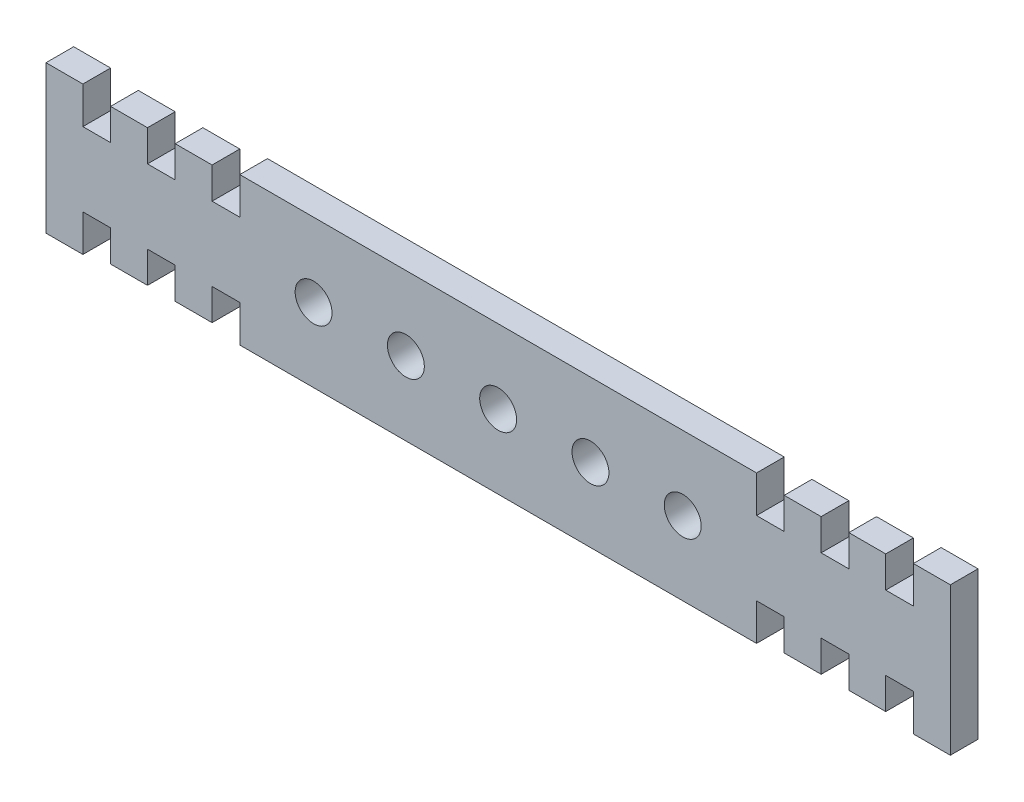
SolidWorks part; units mm, degrees
ref_plane "前视基准面" through (0, 0, 0) normal (0, 0, 1) x (1, 0, 0)
ref_plane "上视基准面" through (0, 0, 0) normal (0, 1, 0) x (1, 0, 0)
ref_plane "右视基准面" through (0, 0, 0) normal (1, 0, 0) x (0, 0, -1)
other "Configuration Table"
sketch "草图1" plane through (0, 0, 0) normal (0, 0, 1) x (1, 0, 0)
  line L0 (-0.124, 0.6439) -> (26.9077, 0.6439) construction
  line L1 (-0.124, -0.5548) -> (-0.124, -17.0412) construction
  line L2 (-14.124, 4.6439) -> (13.8765, 4.6439)
  line L3 (13.8765, 4.6439) -> (13.8765, 2.6439)
  line L4 (20.8755, 2.6439) -> (22.376, 2.6439)
  line L5 (15.376, 2.6439) -> (15.376, 4.3439)
  line L6 (15.376, 4.3439) -> (17.376, 4.3439)
  line L7 (17.376, 4.3439) -> (17.376, 2.6439)
  line L8 (-21.124, 4.3439) -> (-19.1235, 4.3439)
  line L9 (18.8755, 2.6439) -> (18.8755, 4.3439)
  line L10 (18.8755, 4.3439) -> (20.876, 4.3439)
  line L11 (20.8755, 4.3439) -> (20.8755, 2.6439)
  line L12 (-14.124, -3.3561) -> (13.8765, -3.3561)
  line L13 (22.375, 2.6439) -> (22.375, 4.6439)
  line L14 (22.375, 4.6439) -> (24.375, 4.6439)
  line L15 (24.375, 4.6439) -> (24.375, -3.3561)
  line L16 (-22.624, -1.3561) -> (-21.1235, -1.3561)
  line L17 (22.376, -1.3561) -> (22.376, -3.3561)
  line L18 (20.8755, -1.3561) -> (22.376, -1.3561)
  line L19 (20.876, -3.0561) -> (20.876, -1.3561)
  line L20 (18.8755, -3.0561) -> (20.876, -3.0561)
  line L21 (18.876, -1.3561) -> (18.876, -3.0561)
  line L22 (17.376, -1.3561) -> (18.876, -1.3561)
  line L23 (17.376, -3.0561) -> (17.376, -1.3561)
  line L24 (15.376, -3.0561) -> (17.376, -3.0561)
  line L25 (15.376, -1.3561) -> (15.376, -3.0561)
  line L26 (13.876, -1.3561) -> (15.376, -1.3561)
  line L27 (13.876, -3.3561) -> (13.876, -1.3561)
  line L28 (13.876, 2.6439) -> (15.376, 2.6439)
  line L29 (-21.124, -3.0561) -> (-19.1235, -3.0561)
  line L33 (18.876, 2.6439) -> (18.876, 4.3439)
  line L35 (20.876, 4.3439) -> (20.876, 2.6439)
  line L37 (22.376, 2.6439) -> (22.376, 4.6439)
  line L38 (-22.624, 2.6439) -> (-21.1235, 2.6439)
  line L39 (22.375, -3.3561) -> (24.375, -3.3561)
  line L40 (22.375, -1.3561) -> (22.375, -3.3561)
  line L42 (20.8755, -3.0561) -> (20.8755, -1.3561)
  line L45 (18.8755, -1.3561) -> (18.8755, -3.0561)
  line L162 (13.876, 4.6439) -> (13.876, 2.6439)
  line L167 (17.376, 2.6439) -> (18.876, 2.6439)
  line L185 (13.8765, -3.3561) -> (13.8765, -1.3561)
  line L188 (-15.624, -1.3561) -> (-15.624, -3.0561)
  line L189 (-15.624, -3.0561) -> (-17.624, -3.0561)
  line L190 (-17.624, -3.0561) -> (-17.624, -1.3561)
  line L192 (-19.1235, -1.3561) -> (-19.1235, -3.0561)
  line L194 (-21.1235, -3.0561) -> (-21.1235, -1.3561)
  line L196 (-22.6231, -1.3561) -> (-22.6231, -3.3561)
  line L197 (-22.6231, -3.3561) -> (-24.6231, -3.3561)
  line L199 (-22.624, 2.6439) -> (-22.624, 4.6439)
  line L201 (-21.124, 4.3439) -> (-21.124, 2.6439)
  line L203 (-19.124, 2.6439) -> (-19.124, 4.3439)
  line L204 (-17.624, 2.6439) -> (-19.124, 2.6439)
  line L205 (-17.624, 4.3439) -> (-17.624, 2.6439)
  line L206 (-15.624, 4.3439) -> (-17.624, 4.3439)
  line L207 (-15.624, 2.6439) -> (-15.624, 4.3439)
  line L208 (-14.124, 2.6439) -> (-15.624, 2.6439)
  line L213 (-17.624, -1.3561) -> (-19.124, -1.3561)
  line L214 (-19.124, -1.3561) -> (-19.124, -3.0561)
  line L216 (-21.124, -3.0561) -> (-21.124, -1.3561)
  line L218 (-22.624, -1.3561) -> (-22.624, -3.3561)
  line L221 (-22.6231, 2.6439) -> (-22.6231, 4.6439)
  line L223 (-21.1235, 4.3439) -> (-21.1235, 2.6439)
  line L225 (-19.1235, 2.6439) -> (-19.1235, 4.3439)
  line L341 (-14.124, -1.3561) -> (-15.624, -1.3561)
  line L352 (-24.6231, 4.6439) -> (-24.6231, -3.3561)
  line L353 (-22.6231, 4.6439) -> (-24.6231, 4.6439)
  line L364 (-14.1235, 4.6439) -> (-14.124, 2.6439)
  line L365 (-14.1245, -1.3561) -> (-14.1235, -3.3561)
  circle A0 centre (-0.124, 0.6439) radius 1
  circle A1 centre (4.876, 0.6439) radius 1
  circle A2 centre (9.876, 0.6439) radius 1
  circle A3 centre (-5.124, 0.6439) radius 1
  circle A4 centre (-10.124, 0.6439) radius 1
  point P6 (-0.124, -3.3561)
  point P42 (-0.124, 4.6439)
  dimension "D1" = 28
  dimension "D2" = 2
  dimension "D3" = 1.7
extrude "凸台-拉伸1" add sketch "草图1" along normal blind 1.5
